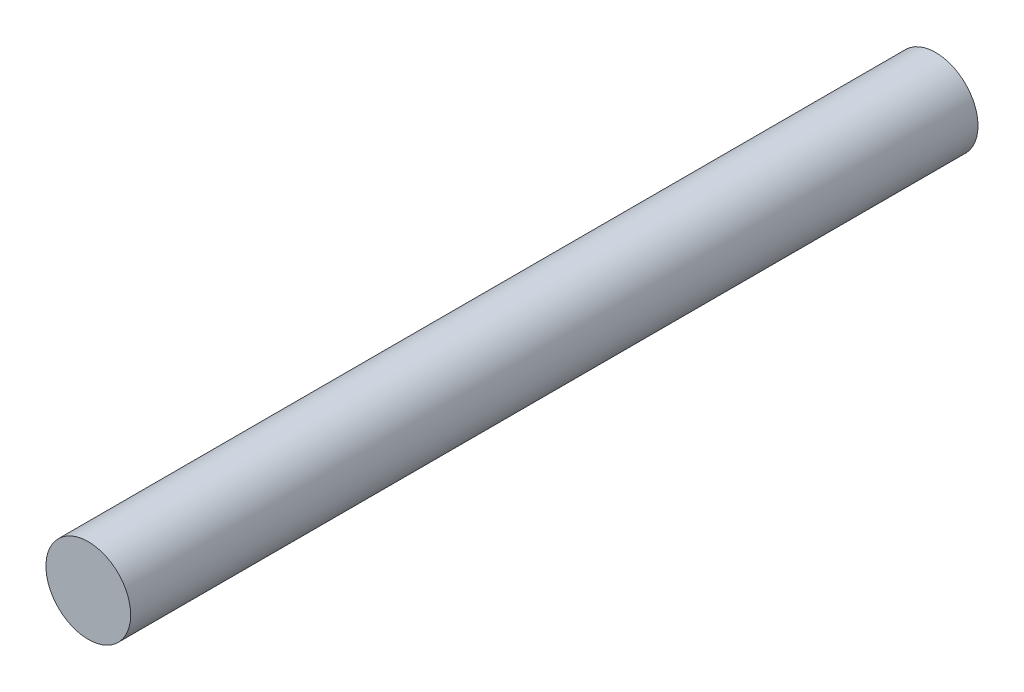
SolidWorks part; units mm, degrees
ref_plane "Front Plane" through (0, 0, 0) normal (0, 0, 1) x (1, 0, 0)
ref_plane "Top Plane" through (0, 0, 0) normal (0, 1, 0) x (1, 0, 0)
ref_plane "Right Plane" through (0, 0, 0) normal (1, 0, 0) x (0, 0, -1)
sketch "Sketch1" plane through (0, 0, 0) normal (0, 0, 1) x (1, 0, 0)
  circle A0 centre (0, 0) radius 2
  dimension "D1" = 4
extrude "Boss-Extrude1" add sketch "Sketch1" along normal blind 40
